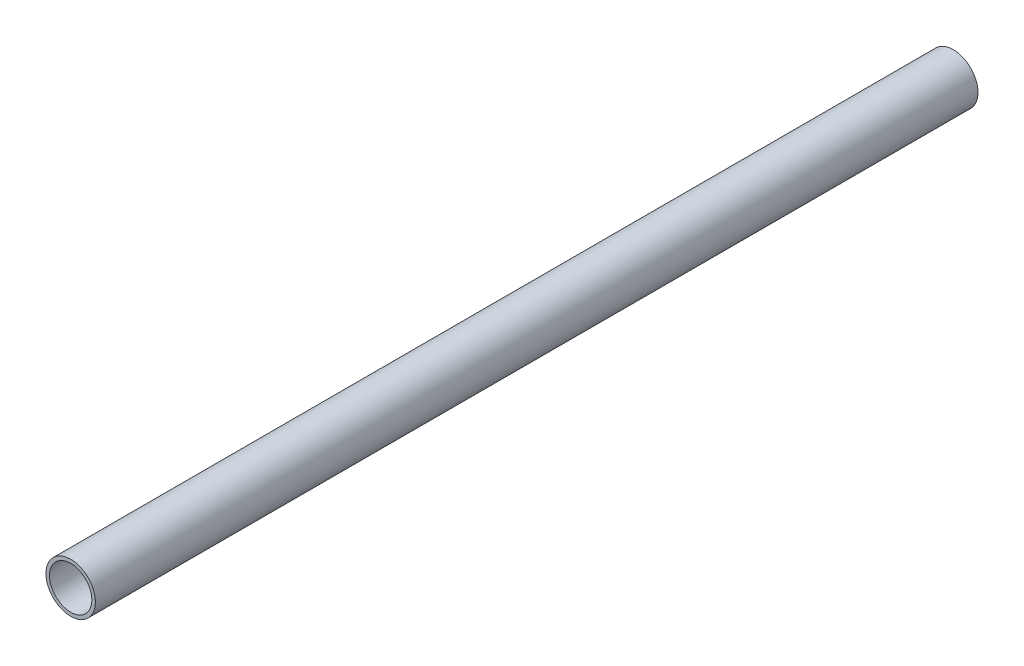
SolidWorks part; units mm, degrees
ref_plane "Спереди" through (0, 0, 0) normal (0, 0, 1) x (1, 0, 0)
ref_plane "Сверху" through (0, 0, 0) normal (0, 1, 0) x (1, 0, 0)
ref_plane "Справа" through (0, 0, 0) normal (1, 0, 0) x (0, 0, -1)
sketch "Эскиз1" plane through (0, 0, 0) normal (0, 0, 1) x (1, 0, 0)
  circle A0 centre (0, 0) radius 14
extrude "Бобышка-Вытянуть1" add sketch "Эскиз1" along normal blind 500
sketch "Эскиз2" plane through (0, 0, 0) normal (0, 0, -1) x (-1, 0, 0)
  circle A0 centre (0, 0) radius 12
extrude "Вырез-Вытянуть1" cut sketch "Эскиз2" against normal through all
